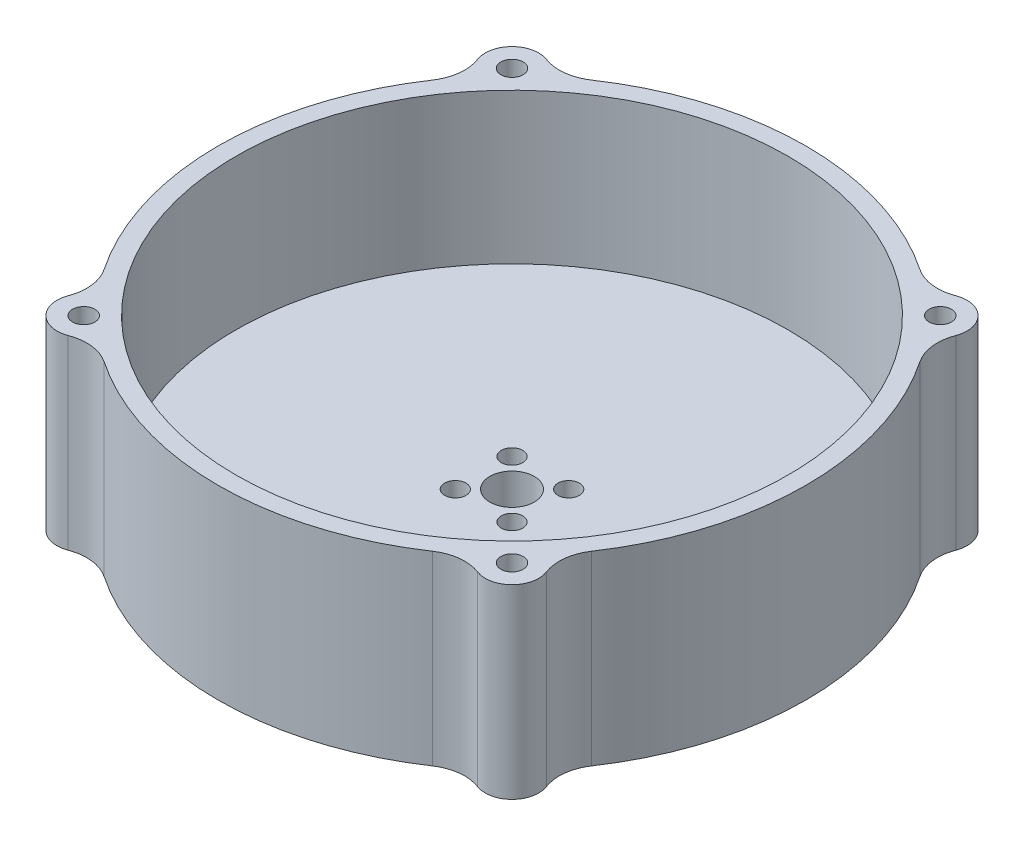
SolidWorks part; units mm, degrees
ref_plane "Front Plane" through (0, 0, 0) normal (0, 0, 1) x (1, 0, 0)
ref_plane "Top Plane" through (0, 0, 0) normal (0, 1, 0) x (1, 0, 0)
ref_plane "Right Plane" through (0, 0, 0) normal (1, 0, 0) x (0, 0, -1)
sketch "Sketch1" plane through (0, 0, 0) normal (0, 1, 0) x (1, 0, 0)
  circle A0 centre (0, 0) radius 33
  dimension "D1" = 66
extrude "Boss-Extrude1" add sketch "Sketch1" along normal blind 4
sketch "Sketch2" plane through (0, 4, 0) normal (0, 1, 0) x (1, 0, 0)
  circle A0 centre (0, 0) radius 31
  circle A1 centre (0, 0) radius 33 construction
  circle A2 centre (0, 0) radius 33
  dimension "D1" = 62
extrude "Boss-Extrude2" add sketch "Sketch2" along normal blind 16.88
sketch "Sketch5" plane through (0, 0, 0) normal (0, -1, 0) x (1, 0, 0)
  line L1 (-3.182, 3.182) -> (3.182, 3.182)
  line L2 (-3.182, 3.182) -> (-3.182, -3.182)
  line L3 (-3.182, -3.182) -> (3.182, -3.182)
  line L4 (3.182, 3.182) -> (3.182, -3.182)
  circle A0 centre (0, 0) radius 4.5
  dimension "D1" = 9
hole_wizard "M2 Clearance Hole1" positions "Sketch6" profile "Sketch8" hole size "M2" standard "ANSI Metric" end condition through all
sketch "Sketch6" plane through (0, 0, 0) normal (0, -1, 0) x (-1, 0, 0)
  point P0 (3.182, 3.182)
  point P3 (3.182, -3.182)
  point P6 (-3.182, -3.182)
  point P9 (-3.182, 3.182)
sketch "Sketch8" plane through (-3.182, 0, -3.182) normal (1, 0, 0) x (0, 0, -1)
  line L0 (0, 0) -> (0, 20.88)
  line L1 (0, 20.88) -> (1.2, 20.88)
  line L2 (1.2, 20.88) -> (1.2, 0)
  line L5 (1.2, 0) -> (0, 0)
  line L11 (0, -6.35) -> (0, 107.95) construction
  dimension "Thru Hole Dia." = 2.4
  dimension "Thru Hole Depth" = 20.88
sketch "Sketch13" plane through (0, 4, 0) normal (0, 1, 0) x (1, 0, 0)
  circle A0 centre (0, 0) radius 2.5
  dimension "D1" = 5
extrude "Cut-Extrude3" cut sketch "Sketch13" against normal through all
sketch "Sketch10" plane through (0, 4, 0) normal (0, 1, 0) x (1, 0, 0)
  line L0 (15, -4) -> (15, 4) construction
  line L1 (13.5, -4) -> (13.5, 4)
  line L2 (16.5, -4) -> (16.5, 4)
  arc A1 (13.5, -4) -> (16.5, -4) centre (15, -4) ccw
  arc A2 (16.5, 4) -> (13.5, 4) centre (15, 4) ccw
  point P2 (15, 0)
  dimension "D1" = 15
  dimension "D2" = 8
  dimension "D3" = 3
extrude "Cut-Extrude2" cut sketch "Sketch10" against normal through all
sketch "Sketch15" plane through (0, 20.88, 0) normal (0, 1, 0) x (1, 0, 0)
  line L0 (0, 0) -> (24.0416, 24.0416) construction
  line L1 (13.5, 4) -> (13.5, -4) construction
  circle A0 centre (24.0416, 24.0416) radius 3
  circle A1 centre (0, 0) radius 31 construction
  dimension "D1" = 6
  dimension "D2" = 45
extrude "Boss-Extrude3" add sketch "Sketch15" against normal through all
fillet "Fillet1" radius 5 2 edges at (25.2199, 10.44, -21.2827) (21.2827, 10.44, -25.2199)
pattern_circular "CirPattern1" count 4 over 360 about axis through (0, 0, 0) along (0, 1, 0) of "Boss-Extrude3", "Fillet1"
hole_wizard "M3x0.5 Tapped Hole1" positions "Sketch18" profile "Sketch19" tap size "M3x0.5" standard "ANSI Metric"
sketch "Sketch18" plane through (0, 20.88, 0) normal (0, 1, 0) x (1, 0, 0)
  point P5 (24.0416, -24.0416)
  point P8 (-24.0416, -24.0416)
  point P14 (-24.0416, 24.0416)
  point P17 (24.0416, 24.0416)
sketch "Sketch19" plane through (24.0416, 20.88, 24.0416) normal (1, 0, 0) x (0, 0, 1)
  line L0 (0, 0) -> (0, 8.2511)
  line L1 (0, 8.2511) -> (1.25, 7.5)
  line L2 (1.25, 7.5) -> (1.25, 0)
  line L5 (1.25, 0) -> (0, 0)
  line L10 (0, 8.2511) -> (-1.25, 7.5) construction
  line L11 (0, -6.35) -> (0, 107.95) construction
  dimension "Tap Drill Dia." = 2.5
  dimension "Tap Drill Depth" = 7.5
  dimension "Drill Angle" = 118
cosmetic thread "Hole Thread1" parameters "D1"=6, "D2"=3
cosmetic thread "Hole Thread2" parameters "D1"=6, "D2"=3
cosmetic thread "Hole Thread3" parameters "D1"=6, "D2"=3
cosmetic thread "Hole Thread4" parameters "D1"=6, "D2"=3
